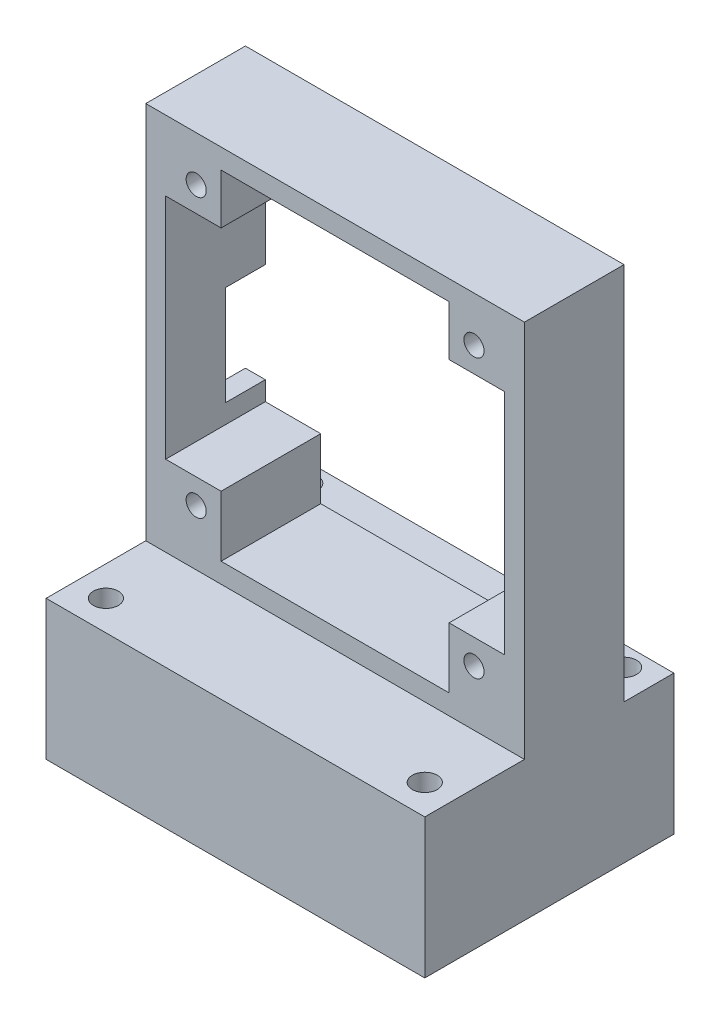
SolidWorks part; units mm, degrees
ref_plane "Front Plane" through (0, 0, 0) normal (0, 0, 1) x (1, 0, 0)
ref_plane "Top Plane" through (0, 0, 0) normal (0, 1, 0) x (1, 0, 0)
ref_plane "Right Plane" through (0, 0, 0) normal (1, 0, 0) x (0, 0, -1)
sketch "Sketch1" plane through (0, 0, 0) normal (0, 1, 0) x (1, 0, 0)
  line L1 (-16.2857, 16.9894) -> (21.7143, 16.9894)
  line L2 (-16.2857, 16.9894) -> (-16.2857, -13.0106)
  line L3 (-16.2857, -13.0106) -> (21.7143, -13.0106)
  line L4 (21.7143, 16.9894) -> (21.7143, -13.0106)
  dimension "D1" = 38
  dimension "D2" = 30
extrude "Boss-Extrude1" add sketch "Sketch1" along normal blind 14
ref_plane "Plane1" through (0, 14, 0) normal (0, 1, 0) x (1, 0, 0)
sketch "Sketch2" plane through (0, 14, 0) normal (0, 1, 0) x (1, 0, 0)
  line L7 (-16.2857, 16.9894) -> (-16.2857, -13.0106) construction
  line L8 (-16.2857, 6.9894) -> (21.7143, 6.9894)
  line L9 (-16.2857, 6.9894) -> (-16.2857, -3.0106)
  line L10 (-16.2857, -3.0106) -> (21.7143, -3.0106)
  line L11 (21.7143, 6.9894) -> (21.7143, -3.0106)
  line L12 (21.7143, -13.0106) -> (21.7143, 16.9894) construction
  dimension "D1" = 10
  dimension "D2" = 10
extrude "Boss-Extrude2" add sketch "Sketch2" along normal blind 38
ref_plane "Plane2" through (0, 0, -6.9894) normal (0, 0, -1) x (-1, 0, 0)
sketch "Sketch3" plane through (0, 0, -6.9894) normal (0, 0, -1) x (-1, 0, 0)
  line L3 (-21.7143, 52) -> (-21.7143, 14) construction
  circle A0 centre (-16.6543, 47.4667) radius 1.01
  circle A1 centre (11.2257, 47.4667) radius 1.01
  circle A2 centre (-16.6543, 19.5867) radius 1.01
  circle A3 centre (11.2257, 19.5867) radius 1.01
  dimension "D3" = 2.02
  dimension "D5" = 27.88
  dimension "D6" = 27.88
  dimension "D7" = 27.88
  dimension "D8" = 27.88
  dimension "D9" = 5.06
extrude "Cut-Extrude1" cut sketch "Sketch3" against normal blind 38
sketch "Sketch4" plane through (0, 0, -6.9894) normal (0, 0, -1) x (-1, 0, 0)
  line L0 (-14.1543, 47.3968) -> (-14.1543, 50)
  line L1 (-14.1543, 50) -> (8.7257, 50)
  line L2 (8.7257, 50) -> (8.7257, 44.9667)
  line L3 (8.7257, 44.9667) -> (14.2857, 44.9667)
  line L4 (14.2857, 44.9667) -> (14.2857, 22.0867)
  line L5 (14.2857, 22.0867) -> (8.7257, 22.0867)
  line L6 (8.7257, 22.0867) -> (8.7257, 16)
  line L7 (8.7257, 16) -> (-14.1543, 16)
  line L8 (-14.1543, 16) -> (-14.1543, 22.0867)
  line L9 (-14.1543, 22.0867) -> (-19.7143, 22.0867)
  line L10 (-19.7143, 22.0867) -> (-19.7143, 44.9667)
  line L11 (-19.7143, 44.9667) -> (-14.1543, 44.9667)
  line L12 (-14.1543, 44.9667) -> (-14.1543, 47.3968)
  line L13 (16.2857, 52) -> (16.2857, 14) construction
  line L14 (-21.7143, 52) -> (-21.7143, 14) construction
  line L15 (-21.7143, 52) -> (16.2857, 52) construction
  line L16 (-21.7143, 14) -> (16.2857, 14) construction
  circle A1 centre (-16.6543, 47.4667) radius 1.01 construction
  circle A2 centre (-16.6543, 19.5867) radius 1.01 construction
  circle A4 centre (11.2257, 19.5867) radius 1.01 construction
  circle A5 centre (11.2257, 47.4667) radius 1.01 construction
  dimension "D1" = 2.5
  dimension "D2" = 2.5
  dimension "D4" = 2.5
  dimension "D5" = 2.5
  dimension "D8" = 2.5
  dimension "D3" = 2.5
  dimension "D6" = 2.5
  dimension "D7" = 2.5
  dimension "D9" = 2
  dimension "D10" = 2
  dimension "D11" = 2
  dimension "D12" = 2
extrude "Cut-Extrude2" cut sketch "Sketch4" against normal blind 38
ref_plane "Plane3" through (-16.2857, 0, 0) normal (-1, 0, 0) x (0, 0, 1)
sketch "Sketch5" plane through (-16.2857, 0, 0) normal (-1, 0, 0) x (0, 0, 1)
  line L0 (-6.9894, 52) -> (-6.9894, 14) construction
  line L1 (-6.9894, 34) -> (-2.9894, 34)
  line L2 (-6.9894, 34) -> (-6.9894, 24)
  line L3 (-6.9894, 24) -> (-2.9894, 24)
  line L4 (-2.9894, 34) -> (-2.9894, 24)
  line L5 (-16.9894, 14) -> (-6.9894, 14) construction
  dimension "D1" = 10
  dimension "D2" = 4
  dimension "D3" = 10
extrude "Cut-Extrude3" cut sketch "Sketch5" against normal blind 12
sketch "Sketch6" plane through (0, 14, 0) normal (0, 1, 0) x (1, 0, 0)
  line L0 (21.7143, 16.9894) -> (-16.2857, 16.9894) construction
  line L1 (-16.2857, 16.9894) -> (-16.2857, 6.9894) construction
  line L2 (21.7143, 6.9894) -> (21.7143, 16.9894) construction
  line L3 (-16.2857, -3.0106) -> (-16.2857, -13.0106) construction
  line L4 (-16.2857, -13.0106) -> (21.7143, -13.0106) construction
  line L5 (21.7143, -13.0106) -> (21.7143, -3.0106) construction
  circle A0 centre (-13.2857, 9.9894) radius 1.25
  circle A1 centre (18.7143, 9.9894) radius 1.25
  circle A2 centre (18.7143, -10.0106) radius 1.25
  circle A3 centre (-13.2857, -10.0106) radius 1.25
  dimension "D1" = 2.5
  dimension "D2" = 7
  dimension "D3" = 3
  dimension "D4" = 7
  dimension "D5" = 3
  dimension "D6" = 3
  dimension "D7" = 3
  dimension "D8" = 3
  dimension "D9" = 3
extrude "Cut-Extrude4" cut sketch "Sketch6" against normal blind 31
sketch "Sketch8" plane through (0, 14, 0) normal (0, 1, 0) x (1, 0, 0)
  line L0 (-16.2857, 16.9894) -> (-16.2857, 6.9894) construction
  line L1 (-16.2857, 11.9894) -> (21.7143, 11.9894)
  line L2 (-16.2857, 11.9894) -> (-16.2857, 16.9894)
  line L3 (-16.2857, 16.9894) -> (21.7143, 16.9894)
  line L4 (21.7143, 11.9894) -> (21.7143, 16.9894)
  line L5 (21.7143, 16.9894) -> (-16.2857, 16.9894) construction
  dimension "D1" = 5
extrude "Cut-Extrude5" cut sketch "Sketch8" against normal blind 31
